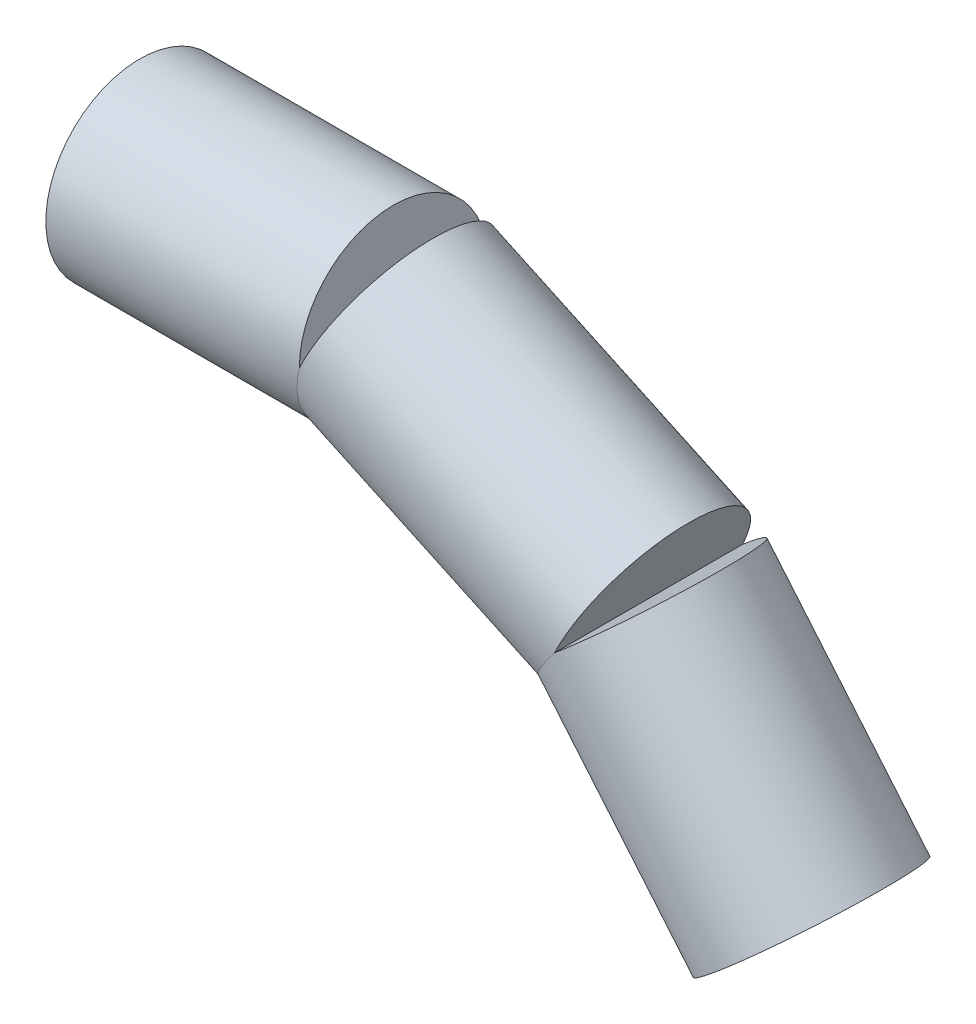
SolidWorks part; units mm, degrees
ref_plane "Front Plane" through (0, 0, 0) normal (0, 0, 1) x (1, 0, 0)
ref_plane "Top Plane" through (0, 0, 0) normal (0, 1, 0) x (1, 0, 0)
ref_plane "Right Plane" through (0, 0, 0) normal (1, 0, 0) x (0, 0, -1)
sketch "U Joint Geometry" plane through (0, 0, 0) normal (0, 0, 1) x (1, 0, 0)
  line L0 (0, 0) -> (45.72, 0)
  line L1 (121.1487, -56.4926) -> (91.7604, -21.469)
  line L2 (45.72, 0) -> (91.7604, -21.469)
  line L3 (45.72, 0) -> (59.2234, 0) construction
  line L4 (121.1487, -56.4926) -> (-16.6151, -56.4926) construction
  line L5 (91.7604, -21.469) -> (111.7736, -30.8013) construction
  dimension "D1" = 45.72
  dimension "D2" = 45.72
  dimension "D3" = 50.8
  dimension "D4" = 25
  dimension "D5" = 50
  dimension "D6" = 25
sketch "Sketch4" plane through (0, 0, 0) normal (1, 0, 0) x (0, 0, -1)
  circle A0 centre (0, 0) radius 16.9545
extrude "Boss-Extrude1" add sketch "Sketch4" along normal up to vertex (45.72 mm away) up to point (45.72, 0, 0)
ref_plane "Plane1" through (0, 0, 0) normal (0, 1, 0) x (1, 0, 0)
ref_plane "Plane3" through (45.72, 0, 0) normal (0.9063, -0.4226, 0) x (0, 0, -1)
sketch "Sketch5" plane through (45.72, 0, 0) normal (0.9063, -0.4226, 0) x (0, 0, -1)
  line L0 (0, 0) -> (0, 5.7068) construction
  line L1 (0, -19.3221) -> (0, 0) construction
  circle A0 centre (0, 0) radius 16.9545
extrude "Boss-Extrude2" add sketch "Sketch5" along normal up to vertex (50.8 mm away) up to point (91.7604, -21.469, 0)
sketch "Sketch7" plane through (0, 0, 0) normal (0, 0, 1) x (1, 0, 0)
  line L0 (0, 0) -> (121.1487, -56.4926)
ref_plane "Plane4" through (91.7604, -21.469, 0) normal (-0.6428, 0.766, 0) x (0.766, 0.6428, 0)
sketch "Sketch9" plane through (91.7604, -21.469, 0) normal (-0.6428, 0.766, 0) x (0.766, 0.6428, 0)
  line L0 (-21.469, 0) -> (0, 0) construction
  circle A0 centre (0, 0) radius 16.9545
extrude "Boss-Extrude3" add sketch "Sketch9" against normal up to vertex (45.72 mm away) up to point (121.1487, -56.4926, 0)
sketch "Sketch10" plane through (77.8729, -92.8053, 0) normal (0.6428, -0.766, 0) x (0.766, 0.6428, 0)
  circle A0 centre (56.4926, 0) radius 9.525
extrude "Cut-Extrude1" cut sketch "Sketch10" against normal blind 12.7
sketch "Sketch12" plane through (0, 0, 0) normal (-1, 0, 0) x (0, 0, 1)
  circle A0 centre (0, 0) radius 9.525
extrude "Cut-Extrude2" cut sketch "Sketch12" against normal blind 12.7
